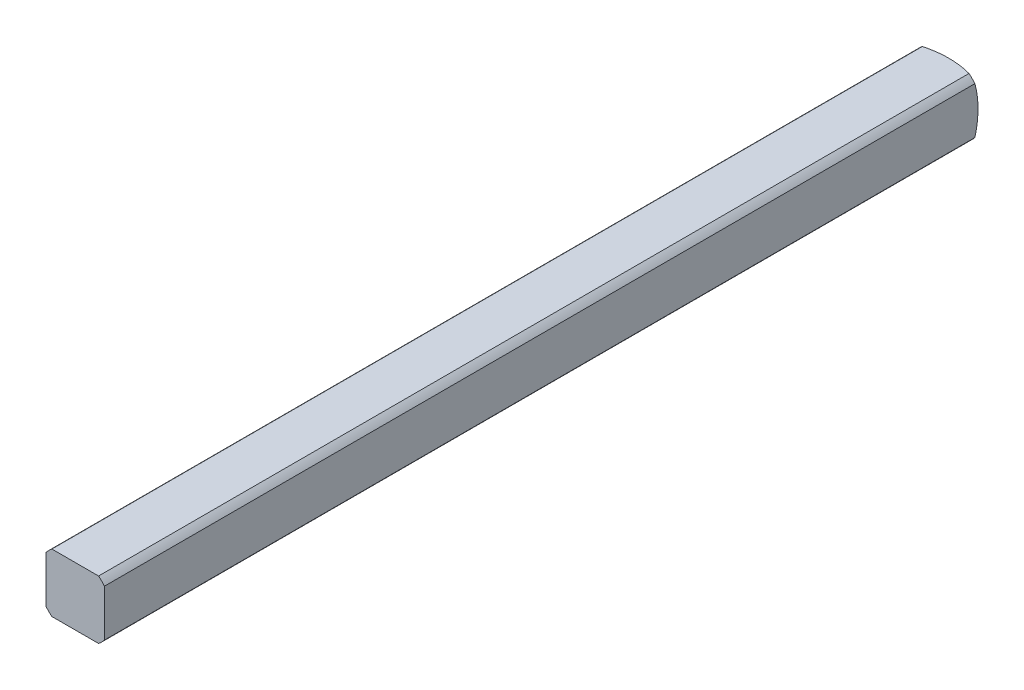
SolidWorks part; units mm, degrees
material "Custom Plastic"
ref_plane "Front Plane" through (0, 0, 0) normal (0, 0, 1) x (1, 0, 0)
ref_plane "Top Plane" through (0, 0, 0) normal (0, 1, 0) x (1, 0, 0)
ref_plane "Right Plane" through (0, 0, 0) normal (1, 0, 0) x (0, 0, -1)
sketch "Sketch1" plane through (0, 0, 0) normal (0, 0, 1) x (1, 0, 0)
  line L0 (-1.5875, -1.5875) -> (1.5875, 1.5875) construction
  line L1 (-1.5875, -1.5875) -> (1.5875, -1.5875)
  line L2 (-1.5875, -1.5875) -> (-1.5875, 1.5875)
  line L3 (-1.5875, 1.5875) -> (1.5875, 1.5875)
  line L4 (1.5875, -1.5875) -> (1.5875, 1.5875)
  dimension "D1" = 3.175
extrude "Boss-Extrude1" add sketch "Sketch1" along normal blind 25.4
sketch "Sketch2" plane through (0, 0, 0) normal (0, 0, -1) x (-1, 0, 0)
  circle A0 centre (0, 0) radius 2.032
  dimension "D1" = 4.064
extrude "Cut-Extrude1" cut sketch "Sketch2" against normal through all flip side to cut
ref_axis "Axis1" through (0, 0, 25.4) along (0, 0, -1)
sketch "Sketch3" plane through (0, 0, 0) normal (0, 1, 0) x (1, 0, 0)
  line L1 (-5.0537, -4.4027) -> (-5.0537, 5.7405)
  line L2 (-5.0537, 5.7405) -> (0, 5.7405)
  line L5 (0, -25.4) -> (0, 0) construction
  line L8 (0, 0.1609) -> (0, 5.7405)
  arc A0 (-5.0537, -4.4027) -> (0, 0.1609) centre (0, -4.9191) cw
  dimension "D1" = 5.08
revolve "Cut-Revolve1" cut sketch "Sketch3" angle 360 about axis through (0, 0, 25.4) along (0, 0, -1)
mirror "Mirror1" about plane through (0, 0, 25.4) normal (0, 0, -1) of bodies 103
sketch "Sketch5" plane through (1.5875, 0, 0) normal (1, 0, 0) x (0, 0, -1)
  line L1 (-50.7065, -1.5875) -> (-47.5315, -1.5875)
  line L2 (-50.7065, 1.5875) -> (-47.5315, 1.5875)
  line L3 (-47.5315, -1.5875) -> (-47.5315, 1.5875)
  line L4 (-50.7065, -1.5875) -> (-51.0398, -1.5875)
  line L5 (-51.0398, -1.5875) -> (-51.0398, 1.5875)
  line L6 (-51.0398, 1.5875) -> (-50.7065, 1.5875)
  dimension "D1" = 3.175
extrude "Cut-Extrude3" cut sketch "Sketch5" against normal through all
